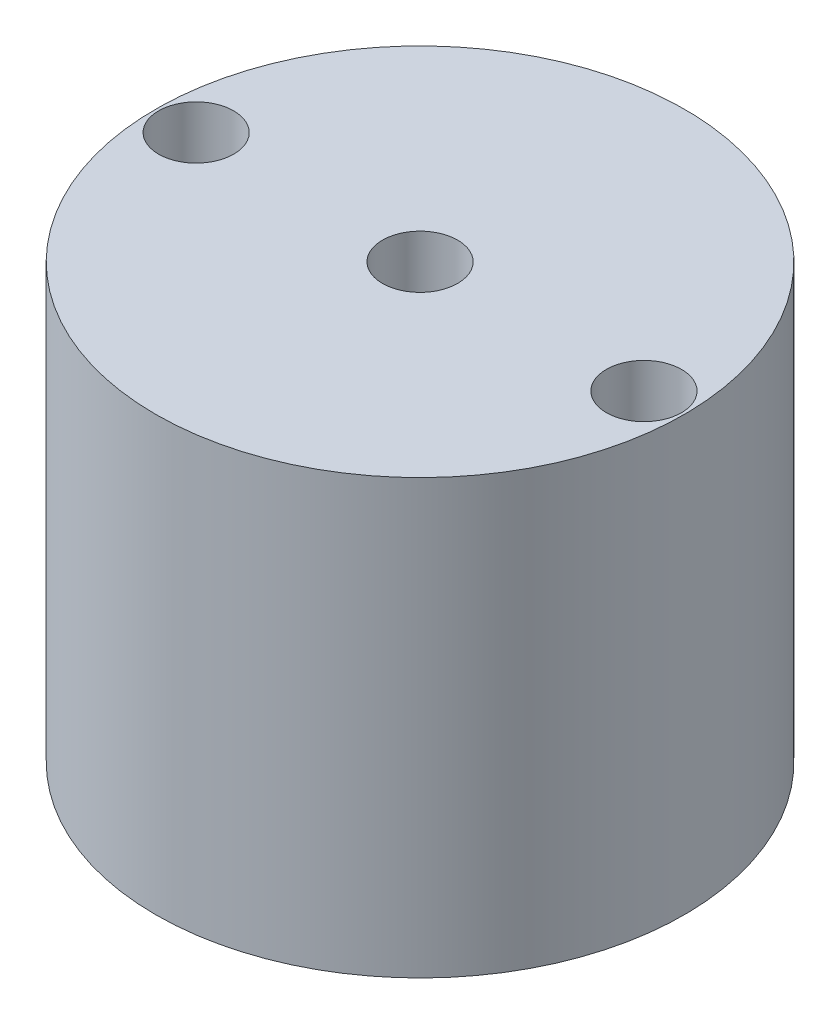
SolidWorks part; units mm, degrees
ref_plane "Front Plane" through (0, 0, 0) normal (0, 0, 1) x (1, 0, 0)
ref_plane "Top Plane" through (0, 0, 0) normal (0, 1, 0) x (1, 0, 0)
ref_plane "Right Plane" through (0, 0, 0) normal (1, 0, 0) x (0, 0, -1)
sketch "Sketch1" plane through (0, 0, 0) normal (0, 1, 0) x (1, 0, 0)
  circle A0 centre (0, 0) radius 23.241
  dimension "D1" = 46.482
extrude "Boss-Extrude1" add sketch "Sketch1" along normal blind 38.1
sketch "Sketch2" plane through (0, 38.1, 0) normal (0, 1, 0) x (1, 0, 0)
  circle A0 centre (19.685, 0) radius 3.302
  circle A1 centre (-19.685, 0) radius 3.302
  dimension "D3" = 6.604
  dimension "D1" = 19.685
  dimension "D2" = 19.685
extrude "Cut-Extrude1" cut sketch "Sketch2" against normal up to next
sketch "Sketch3" plane through (0, 38.1, 0) normal (0, 1, 0) x (1, 0, 0)
  circle A0 centre (0, 0) radius 3.302
  dimension "D1" = 6.604
extrude "Cut-Extrude2" cut sketch "Sketch3" against normal up to next
